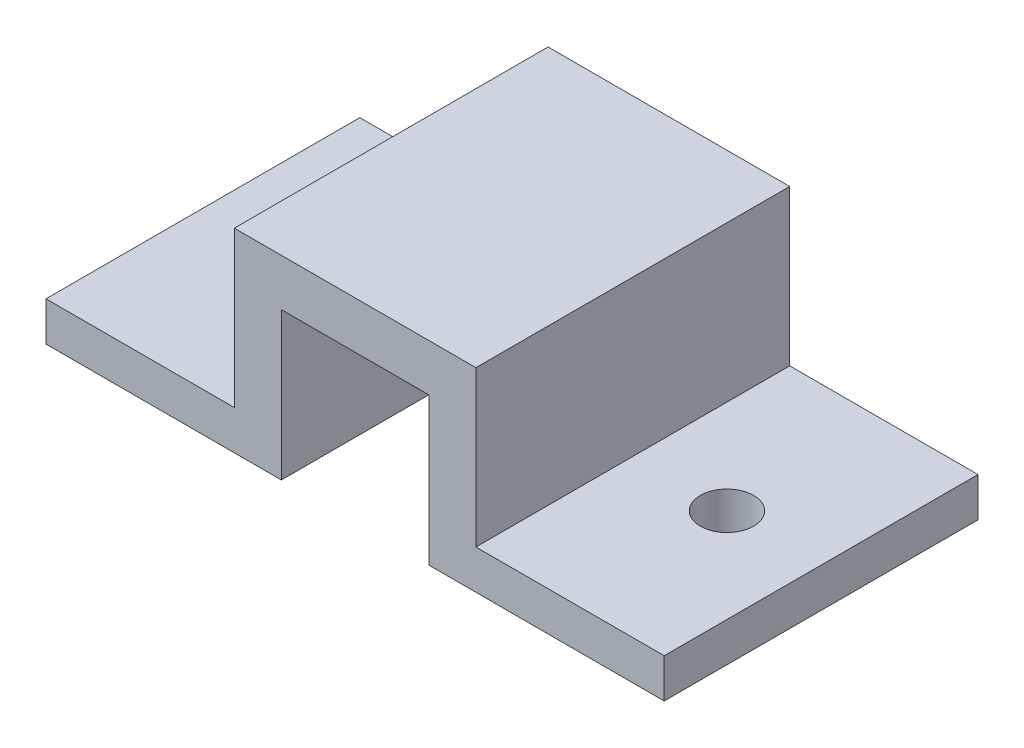
SolidWorks part; units mm, degrees
ref_plane "Front Plane" through (0, 0, 0) normal (0, 0, 1) x (1, 0, 0)
ref_plane "Top Plane" through (0, 0, 0) normal (0, 1, 0) x (1, 0, 0)
ref_plane "Right Plane" through (0, 0, 0) normal (1, 0, 0) x (0, 0, -1)
sketch "Sketch1" plane through (0, 0, 0) normal (0, 0, 1) x (1, 0, 0)
  line L0 (-9.0092, -10.1497) -> (-28.0592, -10.1497)
  line L1 (21.9788, -10.1497) -> (2.9288, -10.1497)
  line L2 (21.9788, -10.1497) -> (21.9788, -6.9747)
  line L4 (-28.0592, -10.1497) -> (-28.0592, -6.9747)
  line L8 (2.9288, -10.1497) -> (2.9288, 1.7883)
  line L9 (2.9288, 1.7883) -> (-9.0092, 1.7883)
  line L10 (-9.0092, -10.1497) -> (-9.0092, 1.7883)
  line L11 (-28.0592, -6.9747) -> (-12.8192, -6.9747)
  line L12 (-12.8192, -6.9747) -> (-12.8192, 5.5983)
  line L13 (-12.8192, 5.5983) -> (6.7388, 5.5983)
  line L14 (6.7388, 5.5983) -> (6.7388, -6.9747)
  line L15 (6.7388, -6.9747) -> (21.9788, -6.9747)
  point P0 (0, 0)
  dimension "D1" = 11.938
  dimension "D2" = 11.938
  dimension "D3" = 3.175
  dimension "D4" = 3.175
  dimension "D5" = 19.05
  dimension "D6" = 19.05
  dimension "D7" = 3.81
  dimension "D8" = 3.81
  dimension "D9" = 3.81
  dimension "D10" = 10.1497
  dimension "D11" = 9.0092
extrude "Boss-Extrude1" add sketch "Sketch1" along normal blind 25.4
sketch "Sketch2" plane through (0, -6.9747, 0) normal (0, 1, 0) x (1, 0, 0)
  line L0 (6.7388, -12.7) -> (21.9788, -12.7) construction
  line L1 (6.7388, -25.4) -> (6.7388, 0) construction
  line L2 (21.9788, -25.4) -> (21.9788, 0) construction
  line L3 (14.3588, -25.4) -> (14.3588, 0) construction
  line L4 (21.9788, -25.4) -> (6.7388, -25.4) construction
  line L5 (21.9788, 0) -> (6.7388, 0) construction
  circle A0 centre (14.3588, -12.7) radius 2.159
  point P15 (14.3588, -12.7)
  dimension "D1" = 4.318
extrude "Cut-Extrude1" cut sketch "Sketch2" against normal blind 25.4 contours A0
sketch "Sketch3" plane through (0, -6.9747, 0) normal (0, 1, 0) x (1, 0, 0)
  line L0 (-20.4392, -25.4) -> (-20.4392, 0) construction
  line L1 (-12.8192, -25.4) -> (-28.0592, -25.4) construction
  line L2 (-12.8192, 0) -> (-28.0592, 0) construction
  line L3 (-12.8192, -12.7) -> (-28.0592, -12.7) construction
  line L4 (-12.8192, -25.4) -> (-12.8192, 0) construction
  line L5 (-28.0592, -25.4) -> (-28.0592, 0) construction
  circle A0 centre (-20.4392, -12.7) radius 2.159
  point P16 (-20.4392, -12.7)
  dimension "D1" = 4.318
extrude "Cut-Extrude2" cut sketch "Sketch3" against normal blind 25.4
